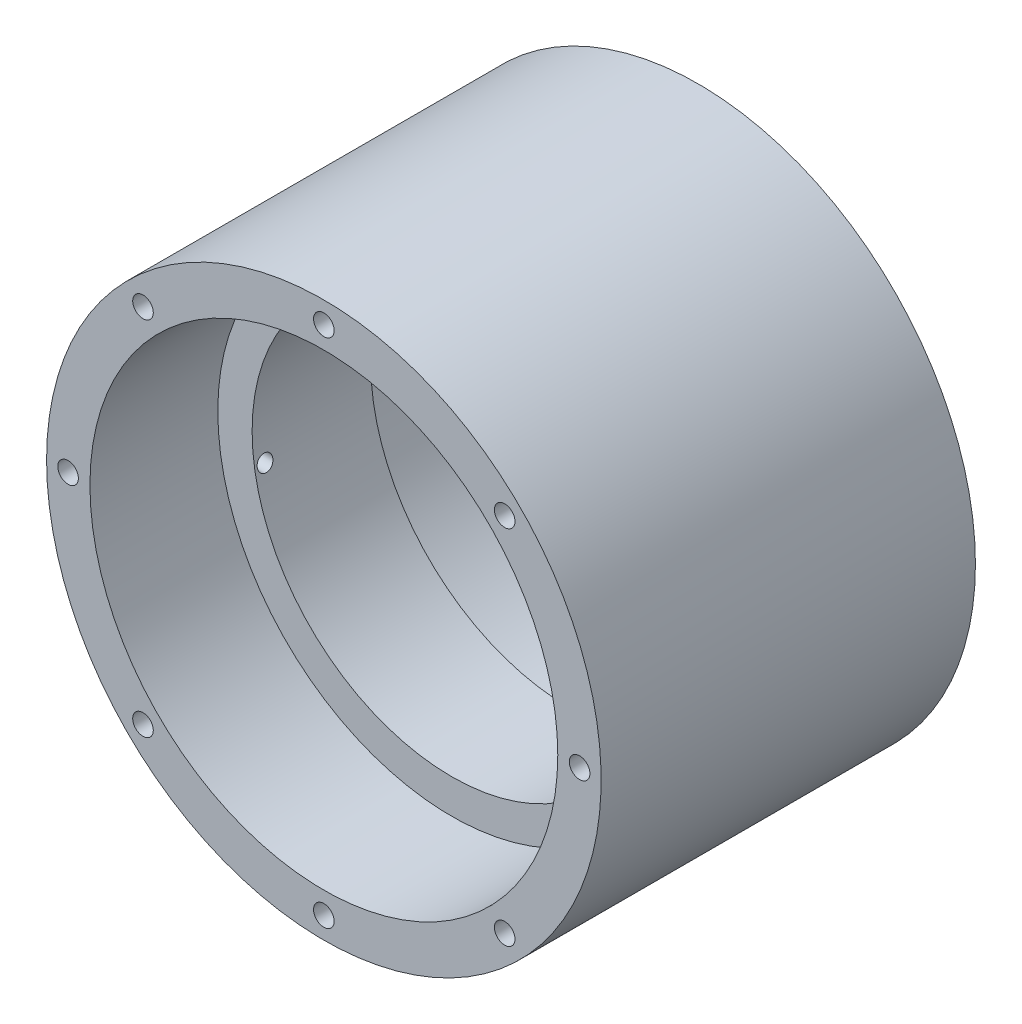
SolidWorks part; units mm, degrees
material "6061-T6 (SS)"
ref_plane "Front Plane" through (0, 0, 0) normal (0, 0, 1) x (1, 0, 0)
ref_plane "Top Plane" through (0, 0, 0) normal (0, 1, 0) x (1, 0, 0)
ref_plane "Right Plane" through (0, 0, 0) normal (1, 0, 0) x (0, 0, -1)
ref_plane "Plane1" through (0, 0, 0) normal (0, -1, 0) x (1, 0, 0)
sketch "Sketch1" plane through (0, 0, 0) normal (0, -1, 0) x (1, 0, 0)
  line L0 (44.45, 60) -> (0, 60)
  line L1 (0, 60) -> (0, 0)
  line L2 (0, 0) -> (44.45, 0)
  line L3 (44.45, 0) -> (44.45, 60)
  line L4 (0, 60) -> (0, 0) construction
revolve "Revolve1" add sketch "Sketch1" angle 360 about L4
sketch "Sketch2" plane through (0, 0, 0) normal (0, 0, -1) x (-1, 0, 0)
  line L0 (43.7242, 8) -> (43.7242, -8)
  arc A0 (43.7242, -8) -> (43.7242, 8) centre (0, 0) ccw
extrude "Cut-Extrude1" cut sketch "Sketch2" against normal blind 50
sketch "Sketch3" plane through (0, 0, 0) normal (0, -1, 0) x (1, 0, 0)
  line L0 (37.5, 60) -> (0, 60)
  line L1 (0, 60) -> (0, 0)
  line L2 (0, 0) -> (37.5, 0)
  line L3 (37.5, 0) -> (37.5, 20.5)
  line L4 (37.5, 20.5) -> (32, 20.5)
  line L5 (32, 20.5) -> (32, 39.5)
  line L6 (32, 39.5) -> (37.5, 39.5)
  line L7 (37.5, 39.5) -> (37.5, 60)
  line L8 (0, 60) -> (0, 0) construction
revolve "Cut-Revolve1" cut sketch "Sketch3" angle 360 about L8
hole_wizard "#4 Clearance Hole1" positions "Sketch5" profile "Sketch4" hole size "#4" standard "ANSI Inch"
sketch "Sketch5" plane through (0, 0, 60) normal (0, 0, 1) x (1, 0, 0)
  point P0 (28.9914, 28.9914)
  point P1 (0, 41)
  point P2 (-28.9914, 28.9914)
  point P3 (-41, 0)
  point P4 (-28.9914, -28.9914)
  point P5 (0, -41)
  point P6 (28.9914, -28.9914)
  point P7 (41, 0)
sketch "Sketch4" plane through (28.9914, 28.9914, 60) normal (1, 0, 0) x (0, -1, 0)
  line L0 (0, 0) -> (0, 8)
  line L1 (0, 8) -> (1.65, 8)
  line L2 (1.65, 8) -> (1.65, 0)
  line L5 (1.65, 0) -> (0, 0)
  line L10 (0, 8) -> (-1.65, 8) construction
  line L11 (0, -6.35) -> (0, 107.95) construction
  dimension "Hole Dia." = 3.3
  dimension "Hole Depth" = 8
  dimension "Drill Angle" = 180
hole_wizard "#2 Clearance Hole1" positions "Sketch7" profile "Sketch6" hole size "#2" standard "ANSI Inch"
sketch "Sketch7" plane through (-43.7242, 0, 0) normal (-1, 0, 0) x (0, 0, 1)
  point P0 (15.5847, 5.15)
sketch "Sketch6" plane through (-43.7242, 5.15, 15.5847) normal (0, 1, 0) x (0, 0, 1)
  line L0 (0, 0) -> (0, 6.5795)
  line L1 (0, 6.5795) -> (1.25, 6.5795)
  line L2 (1.25, 6.5795) -> (1.25, 0)
  line L5 (1.25, 0) -> (0, 0)
  line L11 (0, -6.35) -> (0, 107.95) construction
  dimension "Thru Hole Dia." = 2.5
  dimension "Thru Hole Depth" = 6.5795
hole_wizard "#2 Clearance Hole2" positions "Sketch9" profile "Sketch8" hole size "#2" standard "ANSI Inch"
sketch "Sketch9" plane through (-43.7242, 0, 0) normal (-1, 0, 0) x (0, 0, 1)
  point P0 (37.8347, -5.05)
sketch "Sketch8" plane through (-43.7242, -5.05, 37.8347) normal (0, 1, 0) x (0, 0, 1)
  line L0 (0, 0) -> (0, 12.1252)
  line L1 (0, 12.1252) -> (1.25, 12.1252)
  line L2 (1.25, 12.1252) -> (1.25, 0)
  line L5 (1.25, 0) -> (0, 0)
  line L11 (0, -6.35) -> (0, 107.95) construction
  dimension "Thru Hole Dia." = 2.5
  dimension "Thru Hole Depth" = 12.1252
